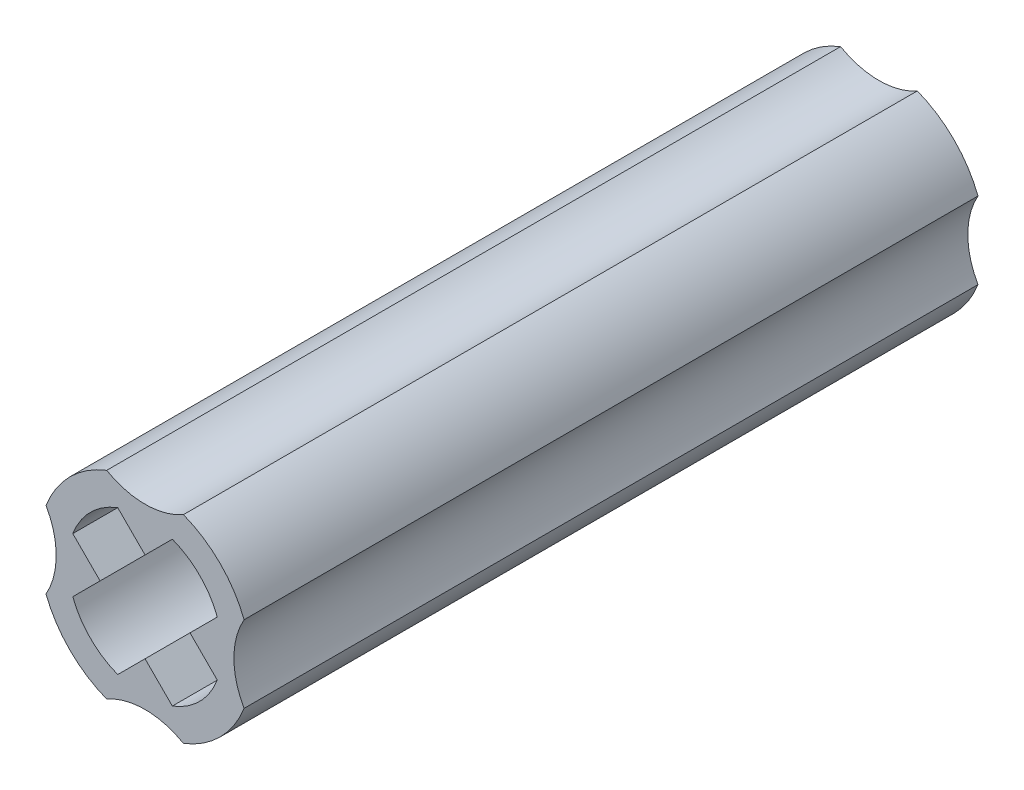
SolidWorks part; units mm, degrees
material "ABS"
ref_plane "Front Plane" through (0, 0, 0) normal (0, 0, 1) x (1, 0, 0)
ref_plane "Top Plane" through (0, 0, 0) normal (0, 1, 0) x (1, 0, 0)
ref_plane "Right Plane" through (0, 0, 0) normal (1, 0, 0) x (0, 0, -1)
sketch "Sketch1" plane through (0, 0, 0) normal (0, 0, 1) x (1, 0, 0)
  line L0 (0, 0) -> (-2.921, 0) construction
  line L1 (-3.4925, 0) -> (-5.461, 0) construction
  arc A0 (-3.2566, -1.2618) -> (-1.2618, -3.2566) centre (0, 0) ccw
  arc A2 (-3.2566, -1.2618) -> (-3.2566, 1.2618) centre (-5.461, 0) ccw
  arc A3 (-1.2618, 3.2566) -> (1.2618, 3.2566) centre (0, 5.461) ccw
  arc A4 (3.2566, 1.2618) -> (3.2566, -1.2618) centre (5.461, 0) ccw
  arc A5 (1.2618, -3.2566) -> (-1.2618, -3.2566) centre (0, -5.461) ccw
  arc A6 (1.2618, -3.2566) -> (3.2566, -1.2618) centre (0, 0) ccw
  arc A7 (3.2566, 1.2618) -> (1.2618, 3.2566) centre (0, 0) ccw
  arc A8 (-1.2618, 3.2566) -> (-3.2566, 1.2618) centre (0, 0) ccw
  point P14 (0, 0)
  dimension "D1" = 6.985
  dimension "D2" = 5.08
  dimension "D3" = 5.461
  dimension "D4" = 4
extrude "Boss-Extrude1" add sketch "Sketch1" along normal mid plane 24.13
sketch "Sketch2" plane through (0, 0, 0) normal (0, 0, 1) x (1, 0, 0)
  line L0 (0, 1.4779) -> (0, -2.54) construction
  line L1 (-0.898, 2.376) -> (0, 1.4779)
  line L2 (0, 1.4779) -> (0.898, 2.376)
  line L3 (2.376, 0.898) -> (1.4779, 0)
  line L4 (1.4779, 0) -> (2.376, -0.898)
  line L5 (0.898, -2.376) -> (0, -1.4779)
  line L6 (0, -1.4779) -> (-0.898, -2.376)
  line L7 (-2.376, -0.898) -> (-1.4779, 0)
  line L8 (-1.4779, 0) -> (-2.376, 0.898)
  arc A0 (-0.898, 2.376) -> (-2.376, 0.898) centre (0, 0) ccw
  arc A1 (2.376, 0.898) -> (0.898, 2.376) centre (0, 0) ccw
  arc A2 (-2.376, -0.898) -> (-0.898, -2.376) centre (0, 0) ccw
  arc A3 (0.898, -2.376) -> (2.376, -0.898) centre (0, 0) ccw
  point P20 (0, 0)
  dimension "D1" = 5.08
  dimension "D2" = 90
  dimension "D3" = 1.27
  dimension "D4" = 1.27
  dimension "D5" = 4
extrude "Cut-Extrude1" cut sketch "Sketch2" against normal through all both and the other way through all
sketch "Sketch3" plane through (0, 0, 0) normal (0, 0, 1) x (1, 0, 0)
  circle A2 centre (0, 0) radius 1.4779
  circle A3 centre (0, 0) radius 2.54
extrude "Boss-Extrude2" add sketch "Sketch3" along normal mid plane 8.255
